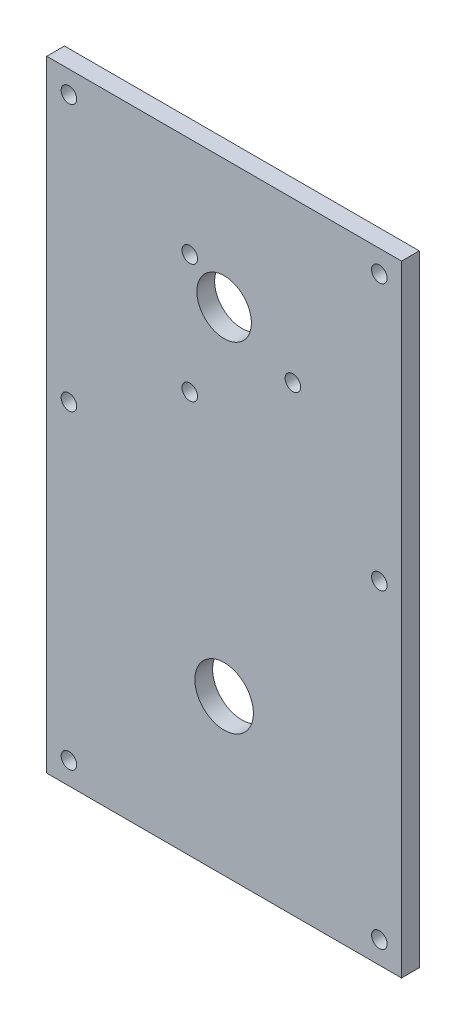
SolidWorks part; units mm, degrees
ref_plane "正面" through (0, 0, 0) normal (0, 0, 1) x (1, 0, 0)
ref_plane "平面" through (0, 0, 0) normal (0, 1, 0) x (1, 0, 0)
ref_plane "右側面" through (0, 0, 0) normal (1, 0, 0) x (0, 0, -1)
sketch "ｽｹｯﾁ1" plane through (0, 0, 0) normal (0, 0, 1) x (1, 0, 0)
  line L0 (40, 0) -> (40, 35)
  line L1 (0, 0) -> (80, 0)
  line L2 (0, 0) -> (0, 140)
  line L3 (0, 140) -> (80, 140)
  line L4 (80, 0) -> (80, 140)
  line L5 (0, 140) -> (5, 140)
  line L6 (0, 140) -> (0, 135)
  line L7 (0, 135) -> (5, 135)
  line L8 (5, 140) -> (5, 135)
  line L9 (80, 0) -> (75, 0)
  line L10 (80, 0) -> (80, 5)
  line L11 (80, 5) -> (75, 5)
  line L12 (75, 0) -> (75, 5)
  line L13 (40, 35) -> (40, 104)
  line L14 (40, 104) -> (55.5, 104)
  line L15 (40, 104) -> (32.25, 117.4234)
  line L16 (40, 104) -> (32.25, 90.5766)
  circle A0 centre (5, 135) radius 1.75
  circle A1 centre (5, 5) radius 1.75
  circle A2 centre (75, 135) radius 1.75
  circle A3 centre (75, 5) radius 1.75
  circle A4 centre (40, 35) radius 6.6
  circle A6 centre (55.5, 104) radius 1.75
  circle A7 centre (32.25, 117.4234) radius 1.75
  circle A8 centre (32.25, 90.5766) radius 1.75
  circle A9 centre (75, 75) radius 1.75
  circle A10 centre (5, 75) radius 1.75
  circle A11 centre (40, 111) radius 6.15
  point P8 (5, 137.5)
  dimension "D7" = 35
  dimension "D8" = 13.2
  dimension "D13" = 7
  dimension "D15" = 40
  dimension "D14" = 135
  dimension "D1" = 80
  dimension "D2" = 140
  dimension "D3" = 5
  dimension "D4" = 5
  dimension "D5" = 5
  dimension "D6" = 5
  dimension "D9" = 69
  dimension "D10" = 15.5
  dimension "D11" = 120
  dimension "D12" = 120
  dimension "D16" = 5
  dimension "D17" = 70
  dimension "D18" = 70
  dimension "D19" = 5
extrude "ﾎﾞｽ - 押し出し1" add sketch "ｽｹｯﾁ1" along normal blind 4
